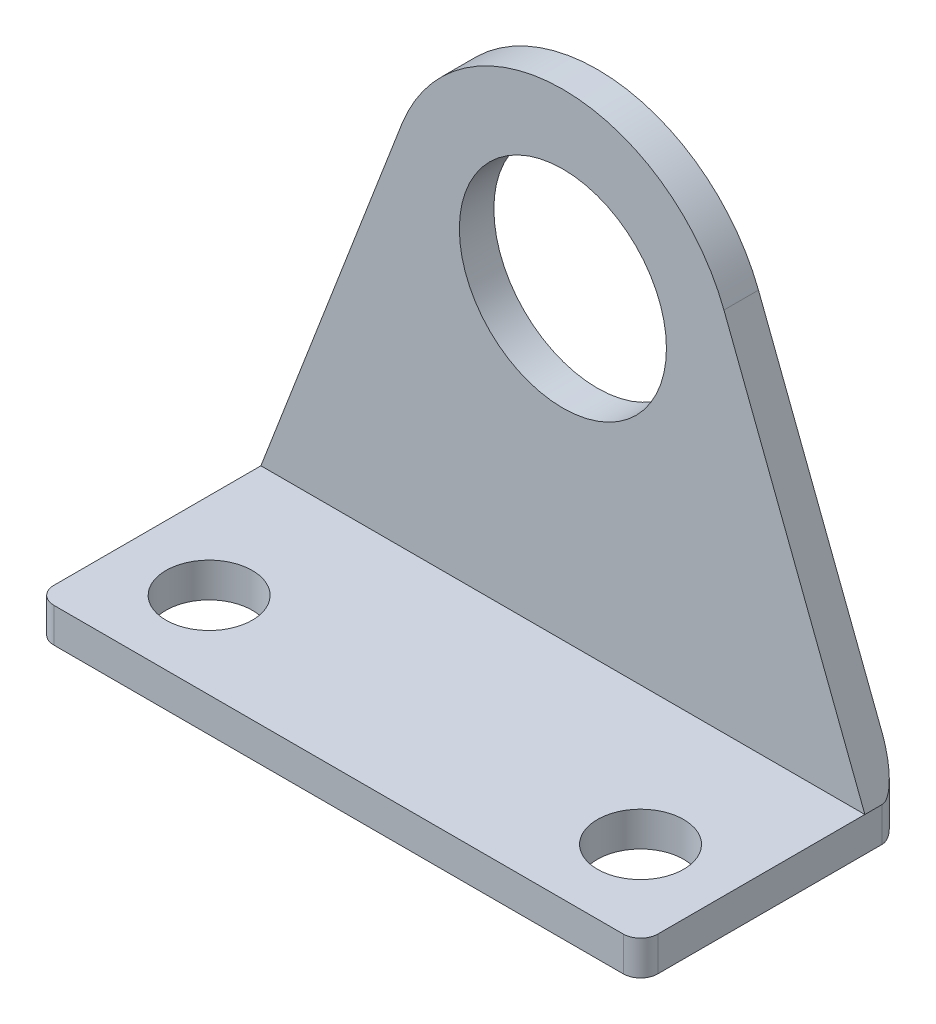
SolidWorks part; units mm, degrees
ref_plane "Front Plane" through (0, 0, 0) normal (0, 0, 1) x (1, 0, 0)
ref_plane "Top Plane" through (0, 0, 0) normal (0, 1, 0) x (1, 0, 0)
ref_plane "Right Plane" through (0, 0, 0) normal (1, 0, 0) x (0, 0, -1)
sketch "Sketch1" plane through (0, 0, 0) normal (0, 1, 0) x (1, 0, 0)
  line L1 (0, 0) -> (35, 0)
  line L2 (0, 0) -> (0, 15)
  line L3 (0, 15) -> (35, 15)
  line L4 (35, 0) -> (35, 15)
  dimension "D1" = 35
  dimension "D2" = 15
extrude "Boss-Extrude1" add sketch "Sketch1" along normal blind 2
sketch "Sketch3" plane through (0, 0, -15) normal (0, 0, -1) x (-1, 0, 0)
  line L5 (0, 2) -> (-35, 2)
  line L9 (-35, 2) -> (-17.5, 47.5)
  line L10 (-17.5, 47.5) -> (0, 2)
  line L11 (-35, 0) -> (0, 0) construction
  point P1 (0, 0)
  point P4 (-17.5, 2)
  dimension "D1" = 47.5
extrude "Boss-Extrude2" add sketch "Sketch3" against normal blind 2
fillet "Fillet1" radius 10 1 edges at (17.5, 47.5, -14)
fillet "Fillet2" radius 1 3 edges at (35, 1, -15) (0, 1, -15) (17.5, 0, -15)
fillet "Fillet3" radius 1 2 edges at (35, 1, 0) (0, 1, 0)
sketch "Sketch4" plane through (0, 2, 0) normal (0, 1, 0) x (1, 0, 0)
  line L0 (0, 13) -> (0, 1) construction
  line L1 (35, 1) -> (35, 13) construction
  line L2 (1, 0) -> (34, 0) construction
  circle A0 centre (5, 5) radius 2.5
  circle A1 centre (30, 5) radius 2.5
  dimension "D1" = 5
  dimension "D2" = 5
  dimension "D3" = 5
  dimension "D4" = 5
  dimension "D5" = 5
  dimension "D6" = 5
extrude "Cut-Extrude1" cut sketch "Sketch4" against normal through all
sketch "Sketch5" plane through (0, 0, -13) normal (0, 0, 1) x (1, 0, 0)
  circle A0 centre (17.5, 19.6432) radius 6
  dimension "D1" = 12
extrude "Cut-Extrude2" cut sketch "Sketch5" against normal through all
